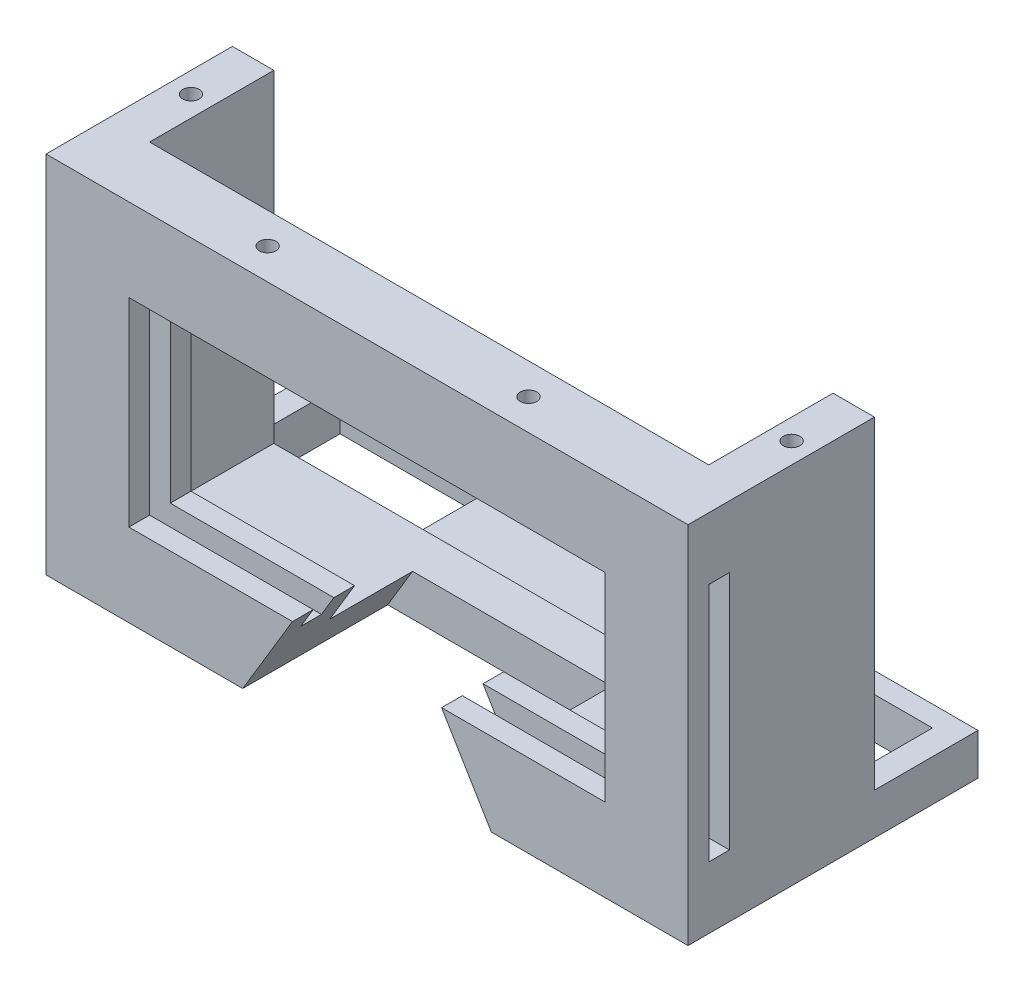
SolidWorks part; units mm, degrees
ref_plane "Front Plane" through (0, 0, 0) normal (0, 0, 1) x (1, 0, 0)
ref_plane "Top Plane" through (0, 0, 0) normal (0, 1, 0) x (1, 0, 0)
ref_plane "Right Plane" through (0, 0, 0) normal (1, 0, 0) x (0, 0, -1)
sketch "Sketch1" plane through (0, 0, 0) normal (0, 1, 0) x (1, 0, 0)
  line L1 (0, 0) -> (155, 0)
  line L2 (0, 0) -> (0, -55)
  line L3 (0, -55) -> (155, -55)
  line L4 (155, 0) -> (155, -55)
  dimension "D1" = 155
  dimension "D2" = 55
extrude "Boss-Extrude1" add sketch "Sketch1" along normal blind 10
sketch "Sketch2" plane through (0, 10, 0) normal (0, 1, 0) x (1, 0, 0)
  line L0 (155, 0) -> (0, 0) construction
  line L1 (6, -5) -> (149, -5)
  line L2 (6, -5) -> (6, -25)
  line L3 (6, -25) -> (149, -25)
  line L4 (149, -5) -> (149, -25)
  line L5 (0, 0) -> (0, -55) construction
  line L6 (155, -55) -> (155, 0) construction
  dimension "D1" = 5
  dimension "D2" = 6
  dimension "D3" = 6
  dimension "D4" = 20
extrude "Cut-Extrude1" cut sketch "Sketch2" against normal blind 5
sketch "Sketch3" plane through (0, 10, 0) normal (0, 1, 0) x (1, 0, 0)
  line L0 (0, 0) -> (0, -55) construction
  line L1 (10, -25) -> (0, -25)
  line L2 (10, -25) -> (10, -55)
  line L3 (10, -55) -> (0, -55)
  line L4 (0, -25) -> (0, -55)
  line L5 (0, -55) -> (155, -55) construction
  line L6 (6, -25) -> (149, -25) construction
  line L7 (155, -55) -> (155, 0) construction
  line L8 (145, -25) -> (155, -25)
  line L9 (145, -25) -> (145, -55)
  line L10 (145, -55) -> (155, -55)
  line L11 (155, -25) -> (155, -55)
  line L12 (6, -25) -> (149, -25) construction
  dimension "D1" = 0
  dimension "D2" = 0
  dimension "D3" = 10
  dimension "D4" = 0
  dimension "D5" = 0
  dimension "D6" = 0
  dimension "D7" = 0
  dimension "D8" = 10
extrude "Boss-Extrude2" add sketch "Sketch3" along normal blind 78
sketch "Sketch4" plane through (0, 5, 0) normal (0, 1, 0) x (1, 0, 0)
  line L0 (6, -5) -> (6, -25) construction
  line L1 (6, -5) -> (41, -5)
  line L2 (6, -5) -> (6, -25)
  line L3 (6, -25) -> (41, -25)
  line L4 (41, -5) -> (41, -25)
  line L5 (99, -5) -> (149, -5)
  line L6 (99, -5) -> (99, -25)
  line L7 (99, -25) -> (149, -25)
  line L8 (149, -5) -> (149, -25)
  line L9 (149, -5) -> (6, -5) construction
  line L10 (6, -25) -> (149, -25) construction
  line L11 (149, -25) -> (149, -5) construction
  dimension "D1" = 0
  dimension "D2" = 0
  dimension "D3" = 0
  dimension "D4" = 35
  dimension "D5" = 0
  dimension "D6" = 0
  dimension "D7" = 0
  dimension "D8" = 50
extrude "Cut-Extrude2" cut sketch "Sketch4" against normal blind 78
sketch "Sketch5" plane through (0, 0, 55) normal (0, 0, 1) x (1, 0, 0)
  line L0 (0, 88) -> (0, 0) construction
  line L1 (0, 88) -> (155, 88)
  line L2 (0, 88) -> (0, 0)
  line L3 (0, 0) -> (155, 0)
  line L4 (155, 88) -> (155, 0)
  line L5 (155, 88) -> (155, 0) construction
  line L6 (0, 88) -> (10, 88) construction
  line L7 (0, 0) -> (155, 0) construction
  dimension "D1" = 0
  dimension "D2" = 0
  dimension "D3" = 0
  dimension "D4" = 0
extrude "Boss-Extrude3" add sketch "Sketch5" along normal blind 15
sketch "Sketch6" plane through (0, 0, 70) normal (0, 0, 1) x (1, 0, 0)
  line L0 (155, 88) -> (0, 88) construction
  line L1 (20, 68) -> (135, 68)
  line L2 (20, 68) -> (20, 20)
  line L3 (20, 20) -> (135, 20)
  line L4 (135, 68) -> (135, 20)
  line L5 (0, 0) -> (155, 0) construction
  line L6 (0, 88) -> (0, 0) construction
  line L7 (155, 0) -> (155, 88) construction
  dimension "D1" = 20
  dimension "D2" = 20
  dimension "D3" = 20
  dimension "D4" = 20
extrude "Cut-Extrude3" cut sketch "Sketch6" against normal blind 20
sketch "Sketch7" plane through (155, 0, 0) normal (1, 0, 0) x (0, 0, -1)
  line L0 (-70, 88) -> (-25, 88) construction
  line L1 (-65, 73) -> (-60, 73)
  line L2 (-65, 73) -> (-65, 15)
  line L3 (-65, 15) -> (-60, 15)
  line L4 (-60, 73) -> (-60, 15)
  line L5 (-70, 0) -> (0, 0) construction
  line L6 (-70, 0) -> (-70, 88) construction
  point P4 (-62.5, 73)
  dimension "D1" = 15
  dimension "D2" = 15
  dimension "D3" = 5
  dimension "D4" = 5
extrude "Cut-Extrude4" cut sketch "Sketch7" against normal blind 200
sketch "Sketch8" plane through (0, 0, 70) normal (0, 0, 1) x (1, 0, 0)
  line L0 (47.5, 0) -> (107.5, 0)
  line L1 (107.5, 0) -> (77.5, 50)
  line L2 (77.5, 50) -> (47.5, 0)
  line L3 (0, 88) -> (0, 0) construction
  line L5 (0, 0) -> (155, 0) construction
  dimension "D1" = 50
  dimension "D2" = 60
  dimension "D3" = 30
  dimension "D4" = 47.5
  dimension "D5" = 0
extrude "Cut-Extrude5" cut sketch "Sketch8" against normal blind 35
sketch "Sketch9" plane through (0, 88, 0) normal (0, 1, 0) x (1, 0, 0)
  line L1 (155, -25) -> (145, -25) construction
  line L2 (10, -25) -> (0, -25) construction
  line L3 (155, -70) -> (155, -25) construction
  line L4 (0, -25) -> (0, -70) construction
  circle A0 centre (150, -40) radius 2
  circle A1 centre (5, -40) radius 2
  dimension "D1" = 4
  dimension "D2" = 4
  dimension "D3" = 15
  dimension "D4" = 15
  dimension "D5" = 5
  dimension "D6" = 5
extrude "Cut-Extrude6" cut sketch "Sketch9" against normal blind 10
sketch "Sketch10" plane through (0, 88, 0) normal (0, 1, 0) x (1, 0, 0)
  line L0 (155, -70) -> (0, -70) construction
  line L1 (155, -70) -> (155, -25) construction
  line L2 (0, -25) -> (0, -70) construction
  circle A0 centre (109, -62.5) radius 2
  circle A1 centre (46, -62.5) radius 2
  dimension "D1" = 4
  dimension "D2" = 4
  dimension "D3" = 7.5
  dimension "D4" = 7.5
  dimension "D5" = 46
  dimension "D6" = 46
extrude "Cut-Extrude7" cut sketch "Sketch10" against normal blind 20
